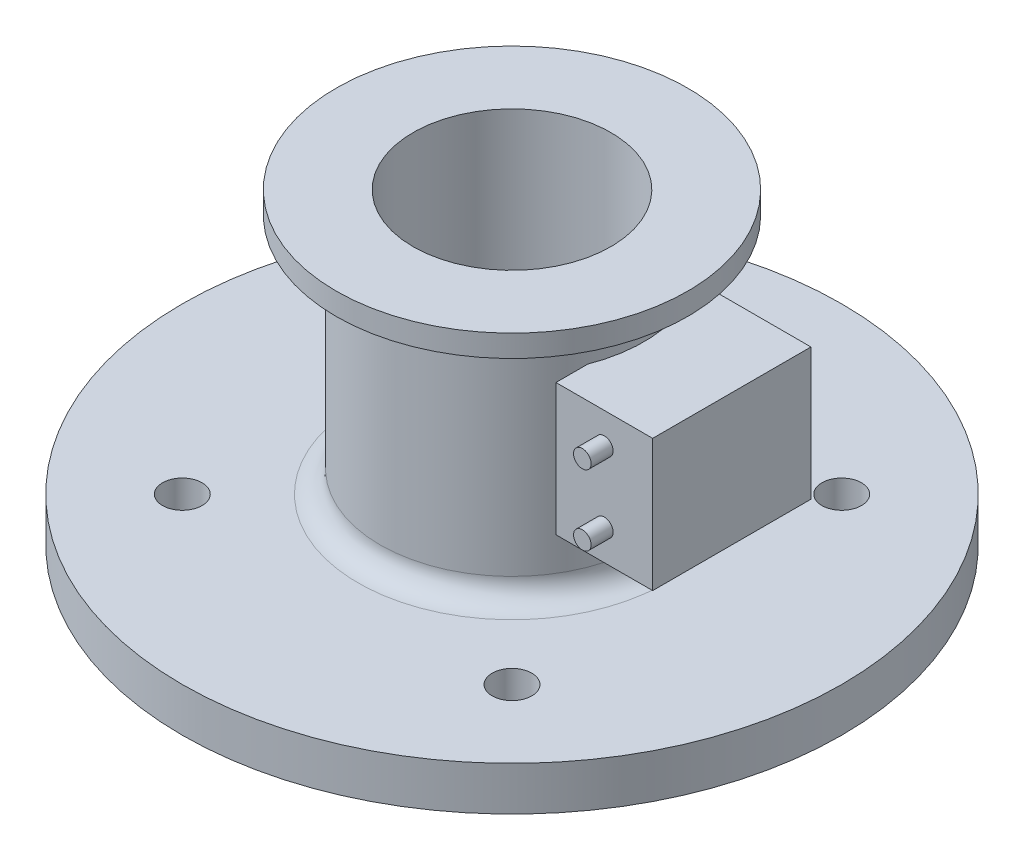
SolidWorks part; units mm, degrees
ref_plane "Ön Düzlem" through (0, 0, 0) normal (0, 0, 1) x (1, 0, 0)
ref_plane "Üst Düzlem" through (0, 0, 0) normal (0, 1, 0) x (1, 0, 0)
ref_plane "Sağ Düzlem" through (0, 0, 0) normal (1, 0, 0) x (0, 0, -1)
sketch "Çizim1" plane through (0, 0, 0) normal (0, 1, 0) x (1, 0, 0)
  line L1 (-50, -50) -> (50, -50)
  line L2 (-50, -50) -> (-50, 50)
  line L3 (-50, 50) -> (50, 50)
  line L4 (50, -50) -> (50, 50)
  line L5 (-50, -50) -> (50, 50) construction
  line L6 (-50, 50) -> (50, -50) construction
  line L7 (-37.5, -37.5) -> (37.5, -37.5) construction
  line L8 (-37.5, -37.5) -> (-37.5, 37.5) construction
  line L9 (-37.5, 37.5) -> (37.5, 37.5) construction
  line L10 (37.5, -37.5) -> (37.5, 37.5) construction
  line L11 (-37.5, -37.5) -> (37.5, 37.5) construction
  line L12 (-37.5, 37.5) -> (37.5, -37.5) construction
  circle A0 centre (-37.5, 37.5) radius 4.5
  circle A1 centre (37.5, 37.5) radius 4.5
  circle A2 centre (37.5, -37.5) radius 4.5
  circle A3 centre (-37.5, -37.5) radius 4.5
  point P0 (0, 0)
  point P5 (0, 0)
  dimension "D1" = 100
  dimension "D4" = 9
  dimension "D2" = 100
  dimension "D3" = 75
extrude "Yükseklik-Ekstrüzyon1" add sketch "Çizim1" along normal blind 10
sketch "Çizim3" plane through (0, 10, 0) normal (0, 1, 0) x (1, 0, 0)
  circle A0 centre (0, 0) radius 30
  circle A1 centre (0, 0) radius 22.5
  dimension "D1" = 60
  dimension "D2" = 45
extrude "Yükseklik-Ekstrüzyon2" add sketch "Çizim3" along normal blind 60
sketch "Çizim4" plane through (0, 70, 0) normal (0, 1, 0) x (1, 0, 0)
  circle A0 centre (0, 0) radius 30
  circle A1 centre (0, 0) radius 40
  dimension "D1" = 80
  dimension "D2" = 60
extrude "Yükseklik-Ekstrüzyon3" add sketch "Çizim4" against normal blind 5
fillet "Radyus1" radius 5 6 edges at (0, 65, 30) (0, 10, -30) (-50, 5, -50) (50, 5, -50) (50, 5, 50) (-50, 5, 50)
sketch "Çizim5" plane through (0, 0, 0) normal (0, 1, 0) x (1, 0, 0)
  line L1 (28, -18) -> (50, -18)
  line L2 (28, -18) -> (28, 18)
  line L3 (28, 18) -> (50, 18)
  line L4 (50, -18) -> (50, 18)
  line L5 (28, -18) -> (50, 18) construction
  line L6 (28, 18) -> (50, -18) construction
  point P0 (39, 0)
  dimension "D1" = 28
  dimension "D2" = 22
  dimension "D3" = 36
extrude "Yükseklik-Ekstrüzyon4" add sketch "Çizim5" along normal mid plane 30 from offset 40 separate body
sketch "Çizim6" plane through (0, 0, 18) normal (0, 0, 1) x (1, 0, 0)
  line L0 (28, 25) -> (50, 25) construction
  line L1 (28, 55) -> (50, 55) construction
  circle A0 centre (39, 48) radius 2
  circle A1 centre (39, 32) radius 2
  point P6 (39, 25)
  dimension "D1" = 7
  dimension "D2" = 7
  dimension "D3" = 4
extrude "Yükseklik-Ekstrüzyon5" add sketch "Çizim6" along normal blind 5
sketch "Çizim7" plane through (0, 0, 0) normal (0, 1, 0) x (1, 0, 0)
  line L4 (45, 50) -> (-45, 50)
  line L5 (-50, 45) -> (-50, -45)
  line L6 (-45, -50) -> (45, -50)
  line L7 (50, -45) -> (50, 45)
  line L8 (45, 50) -> (-45, 50)
  line L9 (-50, 45) -> (-50, -45)
  line L10 (-45, -50) -> (45, -50)
  line L11 (50, -45) -> (50, 45)
  circle A0 centre (0, 0) radius 75
  arc A5 (-45, 50) -> (-50, 45) centre (-45, 45) ccw
  arc A6 (-50, -45) -> (-45, -50) centre (-45, -45) ccw
  arc A7 (45, -50) -> (50, -45) centre (45, -45) ccw
  arc A8 (50, 45) -> (45, 50) centre (45, 45) ccw
  arc A9 (-45, 50) -> (-50, 45) centre (-45, 45) ccw
  arc A10 (-50, -45) -> (-45, -50) centre (-45, -45) ccw
  arc A11 (45, -50) -> (50, -45) centre (45, -45) ccw
  arc A12 (50, 45) -> (45, 50) centre (45, 45) ccw
  dimension "D1" = 0
  dimension "D2" = 150
extrude "Yükseklik-Ekstrüzyon6" add sketch "Çizim7" along normal blind 10
